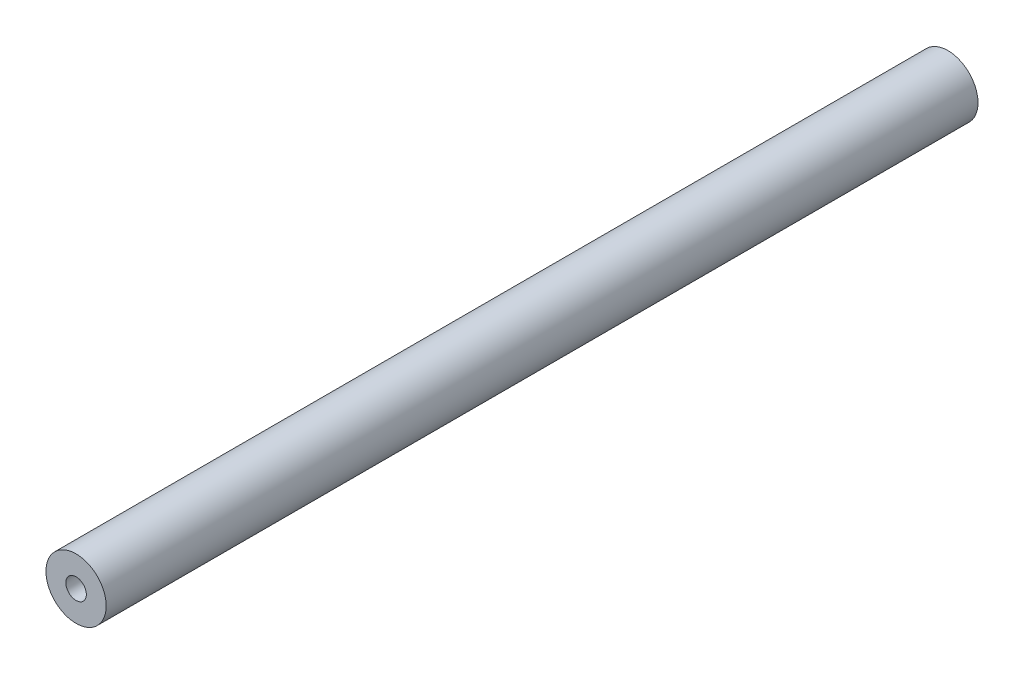
SolidWorks part; units mm, degrees
material "A3钢"
ref_plane "前视基准面" through (0, 0, 0) normal (0, 0, 1) x (1, 0, 0)
ref_plane "上视基准面" through (0, 0, 0) normal (0, 1, 0) x (1, 0, 0)
ref_plane "右视基准面" through (0, 0, 0) normal (1, 0, 0) x (0, 0, -1)
sketch "草图1" plane through (0, 0, 0) normal (0, 0, 1) x (1, 0, 0)
  circle A0 centre (0, 0) radius 15
  dimension "D1" = 30
extrude "凸台-拉伸1" add sketch "草图1" along normal mid plane 434
hole_wizard "M12 螺纹孔1" positions "3D草图1" profile "草图2" tap size "M12" standard "GB"
sketch3d "3D草图1"
  line L0 (0, 0, 217) -> (0, 0, -217) construction
  point P0 (0, 0, 217)
  point P4 (0, 0, -217)
sketch "草图2" plane through (0, 0, 217) normal (1, 0, 0) x (0, -1, 0)
  line L0 (0, 0) -> (0, 32.3144)
  line L1 (0, 32.3144) -> (5.1, 29.25)
  line L2 (5.1, 29.25) -> (5.1, 0)
  line L5 (5.1, 0) -> (0, 0)
  line L10 (0, 32.3144) -> (-5.1, 29.25) construction
  line L11 (0, -6.35) -> (0, 107.95) construction
  dimension "螺纹孔钻头直径" = 10.2
  dimension "螺纹孔钻头深度" = 29.25
  dimension "导头角度" = 118
cosmetic thread "孔螺蚊线1" parameters "D1"=24, "D2"=12
cosmetic thread "孔螺蚊线2" parameters "D1"=24, "D2"=12
